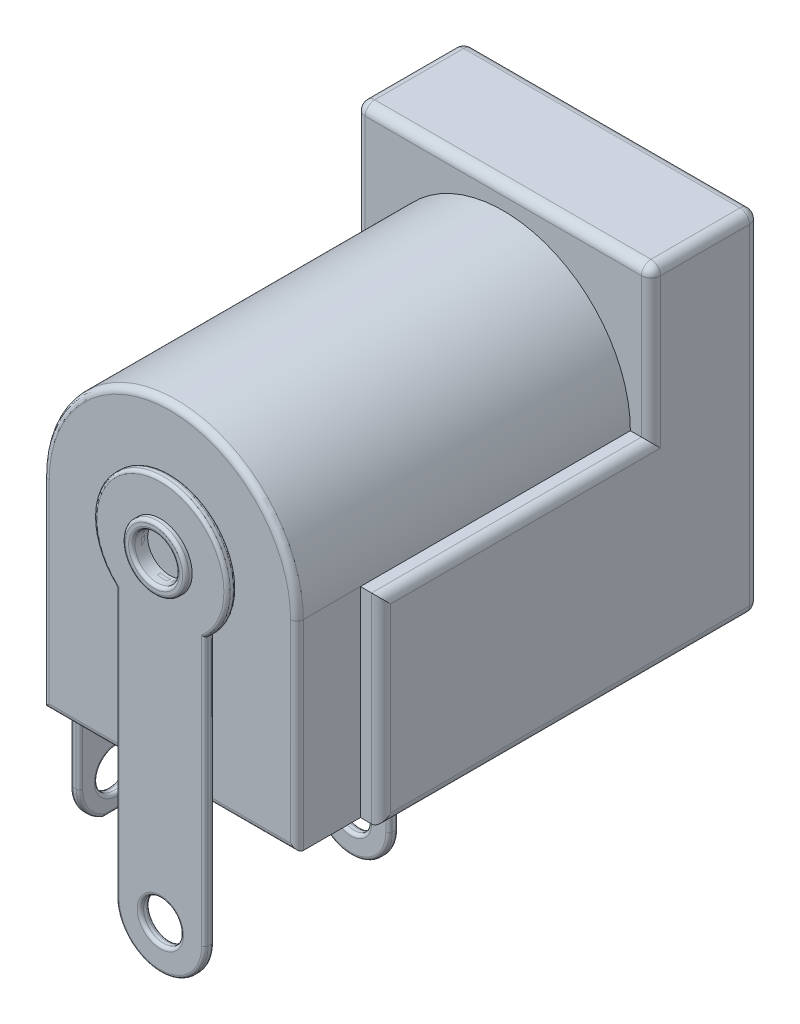
SolidWorks part; units mm, degrees
ref_plane "Front Plane" through (0, 0, 0) normal (0, 0, 1) x (1, 0, 0)
ref_plane "Top Plane" through (0, 0, 0) normal (0, 1, 0) x (1, 0, 0)
ref_plane "Right Plane" through (0, 0, 0) normal (1, 0, 0) x (0, 0, -1)
sketch "Szkic1" plane through (0, 0, 0) normal (0, 0, 1) x (1, 0, 0)
  line L1 (4.65, 5.5) -> (-4.65, 5.5)
  line L2 (4.65, 5.5) -> (4.65, -5.5)
  line L3 (4.65, -5.5) -> (-4.65, -5.5)
  line L4 (-4.65, 5.5) -> (-4.65, -5.5)
  line L5 (4.65, 5.5) -> (-4.65, -5.5) construction
  line L6 (4.65, -5.5) -> (-4.65, 5.5) construction
  point P0 (0, 0)
  dimension "D1" = 11
  dimension "D2" = 9.3
extrude "Dodanie-wyciągnięcie1" add sketch "Szkic1" along normal blind 13.9
sketch "Szkic2" plane through (4.65, 0, 0) normal (1, 0, 0) x (0, 0, -1)
  line L0 (0, -5.5) -> (-11.9, -5.5)
  line L1 (-13.9, -5.5) -> (0, -5.5) construction
  line L2 (-11.9, -5.5) -> (-11.9, 8.0241)
  line L3 (-11.9, 8.0241) -> (-14.6493, 8.0241)
  line L4 (-14.6493, 8.0241) -> (-14.6493, -5.5)
  line L5 (-14.6493, -5.5) -> (-11.9, -5.5)
  dimension "D1" = 11.9
extrude "Wytnij-wyciągnięcie1" cut sketch "Szkic2" against normal blind 0.65 contours L2 L3 L4 L5
mirror "Lustro1" about plane through (0, 0, 0) normal (1, 0, 0) of "Wytnij-wyciągnięcie1"
sketch "Szkic3" plane through (0, 0, 13.9) normal (0, 0, 1) x (1, 0, 0)
  line L14 (-4, 0.8) -> (-6.6118, 0.8)
  line L15 (-6.6118, 0.8) -> (-6.6118, 8.4296)
  line L16 (-6.6118, 8.4296) -> (6.415, 8.4296)
  line L17 (6.415, 8.4296) -> (6.415, 0.8)
  line L18 (6.415, 0.8) -> (4, 0.8)
  arc A1 (4, 0.8) -> (-4, 0.8) centre (0, 0.8) ccw
  point P2 (0, 5.5)
extrude "Wytnij-wyciągnięcie2" cut sketch "Szkic3" against normal blind 10.5
sketch "Szkic4" plane through (0, 0, 0) normal (0, 0, -1) x (-1, 0, 0)
  circle A0 centre (0, 0.8) radius 3.55
  point P2 (0, 5.5)
extrude "Wytnij-wyciągnięcie3" cut sketch "Szkic4" against normal blind 11.9
sketch "Szkic5" plane through (0, 0, 13.9) normal (0, 0, 1) x (1, 0, 0)
  line L0 (-1.4, -0.7652) -> (-1.4, -9.2)
  line L1 (1.4, -9.2) -> (1.4, -0.7652)
  arc A0 (-1.4, -9.2) -> (1.4, -9.2) centre (0, -9.2) ccw
  circle A1 centre (0, -9.2) radius 0.55
  circle A2 centre (0, -9.2) radius 0.63
  arc A3 (1.4, -0.7652) -> (-1.4, -0.7652) centre (0, 0.8) ccw
  circle A4 centre (0, 0.8) radius 0.7
  point P10 (0, 5.5)
  line M8 (-4, -5.5) -> (4, -5.5)
  dimension "D1" = 1.4
extrude "Dodanie-wyciągnięcie2" add sketch "Szkic5" along normal blind 0.3 separate body contours L0 A0 L1 A2 M8 | L1 A3 L0 A4 M8
sketch "Szkic6" plane through (0, 0, 11.9) normal (0, 0, -1) x (-1, 0, 0)
  circle A0 centre (0, 0.8) radius 1
  dimension "D1" = 2
extrude "Dodanie-wyciągnięcie3" add sketch "Szkic6" along normal blind 10 separate body
fillet "Zaokrąglenie1" radius 0.4 1 edges at (-1, 0.8, 1.9)
sketch "Szkic7" plane through (0, 0, 0) normal (1, 0, 0) x (0, 0, -1)
  line L27 (-2.4, -1.4513) -> (-2.4, -1.5746)
  line L28 (-2.5715, -1.3018) -> (-2.5115, -1.3143)
  line L29 (-5.1215, -0.7712) -> (-2.5715, -1.3018)
  line L30 (-7.9, -1.9097) -> (-7.9, -1.4805)
  line L31 (-7.6, -1.9097) -> (-7.9, -1.9097)
  line L32 (-7.6, -1.5759) -> (-7.6, -1.9097)
  line L33 (-2.7, -1.6306) -> (-2.7, -1.5759)
  line L34 (-2.7, -1.5759) -> (-5.15, -1.0652)
  line L36 (-7.9, -1.3375) -> (-5.1785, -0.7712)
  line L37 (-7.9, -1.4805) -> (-7.9, -1.3375)
  line L38 (-5.15, -1.0652) -> (-7.6, -1.5759)
  arc A10 (-2.56, -1.7706) -> (-2.6, -1.7648) centre (-2.56, -1.6306) cw
  arc A11 (-2.4, -1.5746) -> (-2.56, -1.7706) centre (-2.6, -1.5746) cw
  arc A12 (-2.5115, -1.3143) -> (-2.4, -1.4513) centre (-2.54, -1.4513) cw
  arc A13 (-2.6, -1.7648) -> (-2.7, -1.6306) centre (-2.56, -1.6306) cw
  arc A14 (-5.1785, -0.7712) -> (-5.1215, -0.7712) centre (-5.15, -0.9082) cw
  point P22 (3.3376, 0)
  point P23 (0, 0)
  point P24 (0, 0)
extrude "Dodanie-wyciągnięcie4" add sketch "Szkic7" along normal mid plane 2.6 separate body
fillet "Zaokrąglenie2" radius 0.5 1 edges at (-3.55, 0.8, 0)
fillet "Zaokrąglenie3" radius 0.3 15 edges at (4.65, 3.15, 3.4) (4.65, 0.8, 7.65) (4.65, -2.35, 11.9) (4.65, -5.5, 5.95) (0, -5.5, 0) (4.65, 0, 0) (0, 5.5, 3.4) (4.65, 5.5, 1.7) (0, 5.5, 0) (-4.65, 3.15, 3.4) (-4.65, 5.5, 1.7) (-4.65, 0, 0) (-4.65, -5.5, 5.95) (-4.65, -2.35, 11.9) (-4.65, 0.8, 7.65)
fillet "Zaokrąglenie4" radius 0.2 4 edges at (0, -5.5, 13.9) (-4, -2.35, 13.9) (0, 4.8, 13.9) (4, -2.35, 13.9)
fillet "Zaokrąglenie5" radius 0.1 12 edges at (0.7, 0.8, 13.9) (0, -10.6, 13.9) (1.4, -4.9826, 13.9) (0, 2.9, 13.9) (-1.4, -4.9826, 13.9) (0.63, -9.2, 13.9) (0.7, 0.8, 14.2) (0, 2.9, 14.2) (1.4, -4.9826, 14.2) (0, -10.6, 14.2) (-1.4, -4.9826, 14.2) (0.63, -9.2, 14.2)
sketch "Szkic8" plane through (0, 0, 13.9) normal (0, 0, 1) x (1, 0, 0)
  circle A0 centre (0, 0.8) radius 0.7
  circle A1 centre (0, 0.8) radius 1
  dimension "D1" = 2
extrude "Dodanie-wyciągnięcie5" add sketch "Szkic8" along normal blind 0.5
fillet "Zaokrąglenie6" radius 0.1 2 edges at (0.7, 0.8, 14.4) (1, 0.8, 14.4)
ref_plane "Płaszczyzna1" through (0, 0, 7.9) normal (0, 0, -1) x (-1, 0, 0)
sketch "Szkic9" plane through (0, 0, 7.9) normal (0, 0, -1) x (-1, 0, 0)
  line L0 (1.2, -9.2) -> (1.2, -5.5)
  line L1 (1.12, -5.5) -> (1.2, -5.5)
  line L2 (-1.2, -5.5) -> (-1.12, -5.5)
  line L3 (-1.2, -5.5) -> (-1.2, -9.2)
  line L4 (1.12, -5.5) -> (-1.12, -5.5)
  line L5 (4.35, -5.5) -> (-4.35, -5.5) construction
  circle A0 centre (0, -9.2) radius 0.63
  arc A1 (0, -8.65) -> (0.55, -9.2) centre (0, -9.2) ccw
  arc A2 (0.55, -9.2) -> (0, -8.65) centre (0, -9.2) ccw
  arc A3 (-1.2, -9.2) -> (1.2, -9.2) centre (0, -9.2) ccw
  point P6 (0, -5.5)
  point P14 (0, -5.5)
extrude "Dodanie-wyciągnięcie6" add sketch "Szkic9" against normal blind 0.3 separate body contours L3 A3 L0 L1 L4 L2 A0 | A0 A2 A1
fillet "Zaokrąglenie7" radius 0.1 10 edges at (-0.55, -9.2, 7.9) (0, -5.5, 7.9) (-1.2, -7.35, 7.9) (0, -10.4, 7.9) (1.2, -7.35, 7.9) (-0.55, -9.2, 8.2) (0, -10.4, 8.2) (-1.2, -7.35, 8.2) (0, -5.5, 8.2) (1.2, -7.35, 8.2)
sketch "Szkic10" plane through (0, 0, 0) normal (0, 0, -1) x (-1, 0, 0)
  line L0 (4.85, -9.2) -> (4.85, -10.32)
  line L4 (5.15, -10.32) -> (5.15, -9.2)
  line L5 (4.85, -1.9) -> (4.85, -9.2)
  line L6 (5.15, -9.2) -> (5.15, -1.7)
  line L7 (4.65, -1.5) -> (4.65, -1.4036)
  line L8 (4.65, -1.28) -> (4.65, -1.4036)
  line L9 (4.65, -1.28) -> (4.65, -1.2)
  line L10 (-4.35, 5.5) -> (4.35, 5.5) construction
  line L11 (5.15, -10.32) -> (4.85, -10.32)
  arc A0 (4.85, -1.9) -> (4.65, -1.5) centre (4.35, -1.9) ccw
  arc A1 (5.15, -1.7) -> (4.65, -1.2) centre (4.65, -1.7) ccw
  point P2 (0, 5.5)
  point P17 (0, 5.5)
extrude "Dodanie-wyciągnięcie7" add sketch "Szkic10" against normal blind 20.3 separate body
sketch "Szkic11" plane through (-5.15, 0, 0) normal (-1, 0, 0) x (0, 0, 1)
  line L0 (11.9, -9.2) -> (11.9, -1.7)
  line L1 (11.9, -1.7) -> (11.9, -1.28)
  line L2 (9.5, -1.7) -> (9.5, -9.2)
  line L3 (9.5, -1.28) -> (9.5, -1.7)
  line L4 (11.4, -1.2) -> (9.58, -1.2)
  line L5 (11.82, -1.2) -> (11.4, -1.2)
  line L6 (0, -5.2) -> (0, 5.2) construction
  line L7 (9.5, -1.28) -> (9.5, -1.2)
  line L8 (9.5, -1.2) -> (9.58, -1.2)
  line L9 (11.82, -1.2) -> (11.9, -1.2)
  line L10 (11.9, -5.5) -> (11.9, 0.8) construction
  line L11 (11.9, -1.2) -> (11.9, -1.28)
  arc A0 (9.5, -9.2) -> (11.9, -9.2) centre (10.7, -9.2) ccw
  circle A2 centre (10.7, -9.2) radius 0.63
  point P11 (0, 0)
  point P17 (0, 0)
extrude "Wytnij-wyciągnięcie4" cut sketch "Szkic11" against normal blind 20.3 flip side to cut
fillet "Zaokrąglenie8" radius 0.1 16 edges at (-4.7972, -1.6764, 11.9) (-4.7972, -1.6764, 9.5) (-5.0036, -1.3464, 11.9) (-5.0036, -1.3464, 9.5) (-4.85, -9.8793, 11.6892) (-4.85, -5.55, 11.9) (-4.85, -5.55, 9.5) (-4.85, -9.8793, 9.7108) (-4.85, -10.32, 10.7) (-4.85, -8.57, 10.7) (-5.15, -5.45, 11.9) (-5.15, -9.8793, 11.6892) (-5.15, -10.32, 10.7) (-5.15, -9.8793, 9.7108) (-5.15, -5.45, 9.5) (-5.15, -9.83, 10.7)
